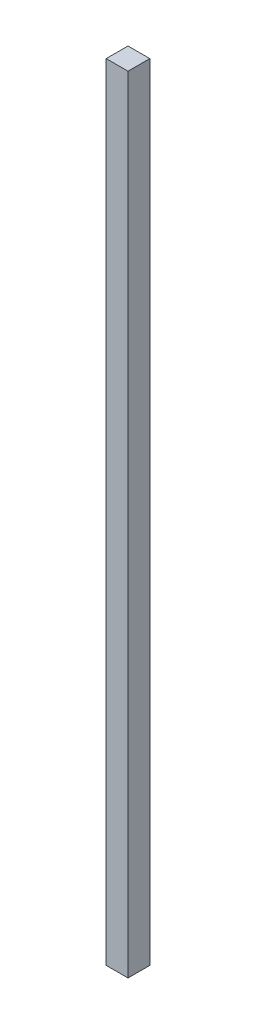
SolidWorks part; units mm, degrees
ref_plane "Front Plane" through (0, 0, 0) normal (0, 0, 1) x (1, 0, 0)
ref_plane "Top Plane" through (0, 0, 0) normal (0, 1, 0) x (1, 0, 0)
ref_plane "Right Plane" through (0, 0, 0) normal (1, 0, 0) x (0, 0, -1)
sketch "Sketch2" plane through (0, 0, 0) normal (0, 0, 1) x (1, 0, 0)
  line L1 (-1.5875, -57.1602) -> (1.5875, -57.1602)
  line L2 (-1.5875, -57.1602) -> (-1.5875, 57.1602)
  line L3 (-1.5875, 57.1602) -> (1.5875, 57.1602)
  line L4 (1.5875, -57.1602) -> (1.5875, 57.1602)
  line L5 (-1.5875, -57.1602) -> (1.5875, 57.1602) construction
  line L6 (-1.5875, 57.1602) -> (1.5875, -57.1602) construction
  point P0 (0, 0)
  dimension "D1" = 3.175
  dimension "D2" = 114.3203
extrude "Boss-Extrude1" add sketch "Sketch2" along normal blind 3.175
equation "\"side thickness\"= 1 / 8in"
equation "\"extrude thickness\"= 1 / 8in"
equation "\"length\"= 4.4528 + 0.048in"
equation "\"D1@Sketch2\"=\"side thickness\""
equation "\"D2@Sketch2\"=\"length\""
equation "\"D1@Boss-Extrude1\"=\"extrude thickness\""
